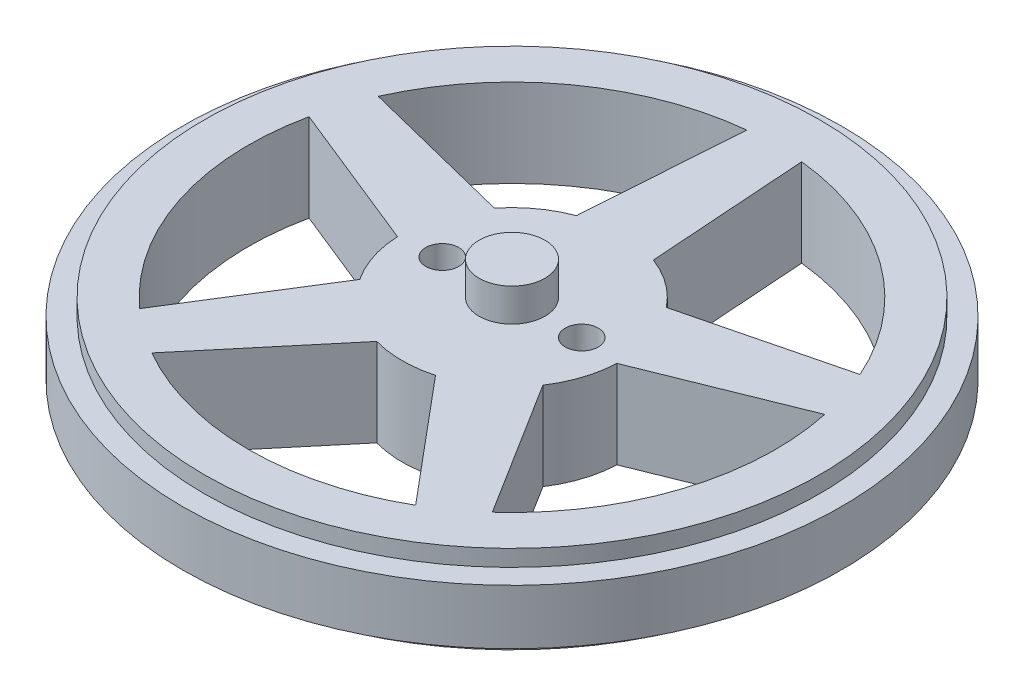
SolidWorks part; units mm, degrees
ref_plane "Front Plane" through (0, 0, 0) normal (0, 0, 1) x (1, 0, 0)
ref_plane "Top Plane" through (0, 0, 0) normal (0, 1, 0) x (1, 0, 0)
ref_plane "Right Plane" through (0, 0, 0) normal (1, 0, 0) x (0, 0, -1)
sketch "Sketch1" plane through (0, 0, 0) normal (0, 1, 0) x (1, 0, 0)
  line L0 (-2.5, 23.8694) -> (-3.5, 9.3675)
  line L1 (3.5, 9.3675) -> (2.5, 23.8694)
  line L2 (7.8275, 6.2234) -> (21.9286, 9.7537)
  line L3 (9.9906, -0.434) -> (23.4737, 4.9984)
  line L4 (8.3376, -5.5212) -> (16.0526, -17.8413)
  line L5 (2.6745, -9.6357) -> (12.0076, -20.7802)
  line L6 (-8.3376, -5.5212) -> (-16.0526, -17.8413)
  line L7 (-2.6745, -9.6357) -> (-12.0076, -20.7802)
  line L8 (-9.9906, -0.434) -> (-23.4737, 4.9984)
  line L9 (-7.8275, 6.2234) -> (-21.9286, 9.7537)
  line L10 (0, 0) -> (0, 28) construction
  line L11 (0, 0) -> (26.6296, 8.6525) construction
  line L12 (0, 0) -> (16.458, -22.6525) construction
  line L13 (0, 0) -> (-16.458, -22.6525) construction
  line L14 (0, 0) -> (-26.6296, 8.6525) construction
  circle A0 centre (0, 0) radius 28
  arc A1 (-9.9906, -0.434) -> (-8.3376, -5.5212) centre (0, 0) ccw
  arc A2 (-2.5, 23.8694) -> (-21.9286, 9.7537) centre (0, 0) ccw
  arc A3 (21.9286, 9.7537) -> (2.5, 23.8694) centre (0, 0) ccw
  arc A4 (16.0526, -17.8413) -> (23.4737, 4.9984) centre (0, 0) ccw
  arc A5 (-12.0076, -20.7802) -> (12.0076, -20.7802) centre (0, 0) ccw
  arc A6 (-23.4737, 4.9984) -> (-16.0526, -17.8413) centre (0, 0) ccw
  arc A7 (-3.5, 9.3675) -> (-7.8275, 6.2234) centre (0, 0) ccw
  arc A8 (7.8275, 6.2234) -> (3.5, 9.3675) centre (0, 0) ccw
  arc A9 (8.3376, -5.5212) -> (9.9906, -0.434) centre (0, 0) ccw
  arc A10 (-2.6745, -9.6357) -> (2.6745, -9.6357) centre (0, 0) ccw
  dimension "D1" = 56
  dimension "D2" = 20
  dimension "D3" = 48
  dimension "D4" = 72
  dimension "D5" = 72
  dimension "D6" = 72
  dimension "D7" = 72
  dimension "D8" = 5
  dimension "D9" = 7
  dimension "D10" = 5
  dimension "D11" = 7
  dimension "D12" = 5
  dimension "D13" = 7
  dimension "D14" = 5
  dimension "D15" = 7
  dimension "D16" = 5
  dimension "D17" = 7
extrude "Boss-Extrude1" add sketch "Sketch1" along normal blind 8
sketch "Sketch2" plane through (0, 8, 0) normal (0, 1, 0) x (1, 0, 0)
  line L0 (-6.35, 0) -> (6.35, 0) construction
  circle A0 centre (-6.35, 0) radius 1.5
  circle A1 centre (6.35, 0) radius 1.5
  dimension "D2" = 3
  dimension "D1" = 12.7
extrude "Cut-Extrude1" cut sketch "Sketch2" against normal up to surface (8 mm away) up to face at (0, 0, 16.104)
sketch "Sketch3" plane through (0, 0, 0) normal (1, 0, 0) x (0, 0, -1)
  line L0 (28, 6.5) -> (30, 6.5)
  line L1 (28, 0) -> (28, 8) construction
  line L2 (30, 6.5) -> (30, 1.5)
  line L3 (30, 1.5) -> (28, 1.5)
  line L4 (28, 0) -> (28, 8) construction
  line L5 (28, 1.5) -> (28, 6.5)
  line L6 (30, 4) -> (28, 4) construction
  line L7 (28, 0) -> (28, 8) construction
  dimension "D1" = 2
  dimension "D2" = 5
sweep "Sweep1" add profiles "Sketch3" path edge at (0, 8, 28)
sketch "Sketch4" plane through (0, 8, 0) normal (0, 1, 0) x (1, 0, 0)
  circle A0 centre (0, 0) radius 3
  dimension "D1" = 6
extrude "Boss-Extrude2" add sketch "Sketch4" along normal blind 3
